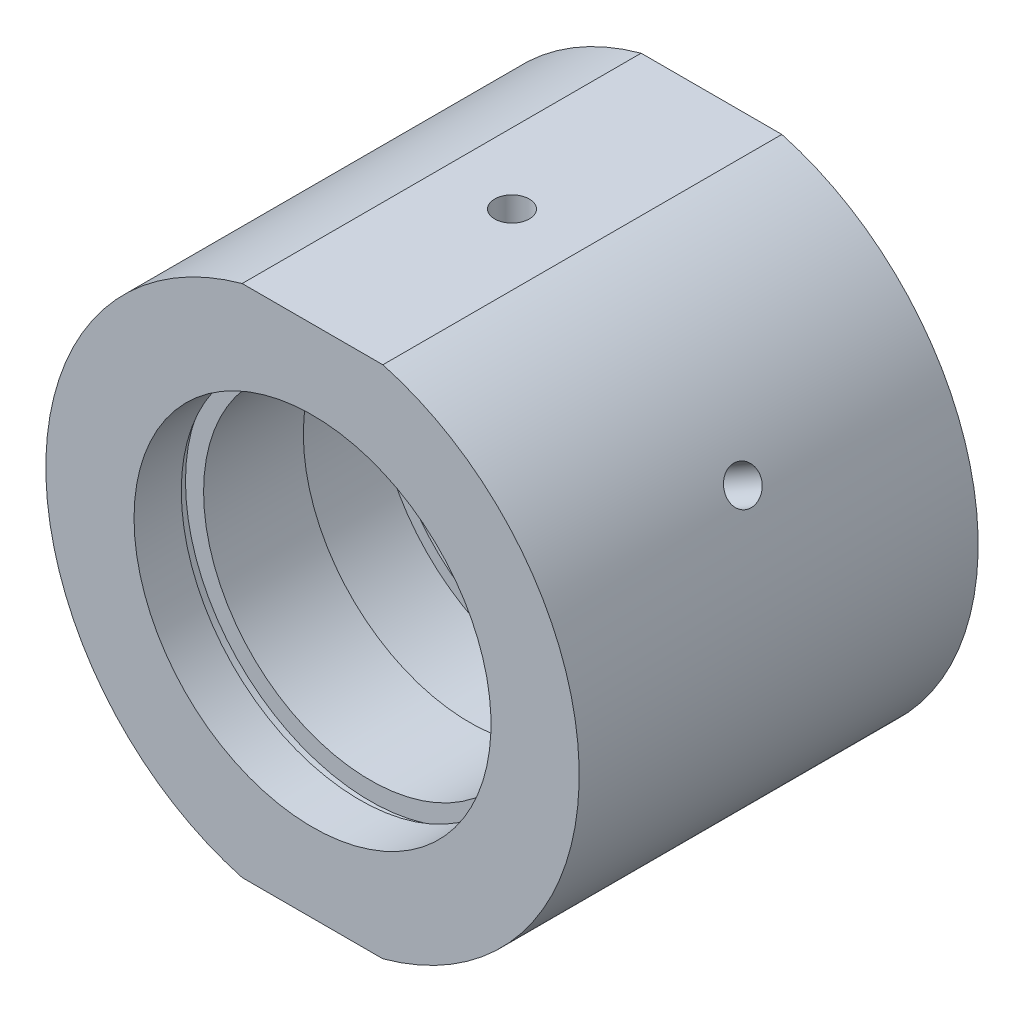
SolidWorks part; units mm, degrees
ref_plane "前视基准面" through (0, 0, 0) normal (0, 0, 1) x (1, 0, 0)
ref_plane "上视基准面" through (0, 0, 0) normal (0, 1, 0) x (1, 0, 0)
ref_plane "右视基准面" through (0, 0, 0) normal (1, 0, 0) x (0, 0, -1)
sketch "草图1" plane through (0, 0, 0) normal (0, 1, 0) x (1, 0, 0)
  line L0 (0, 31.9391) -> (0, -26.491) construction
  line L1 (25.4, 19) -> (25.4, -19)
  line L2 (25.4, -19) -> (17, -19)
  line L3 (17, -19) -> (17, -14.5)
  line L4 (17, -14.5) -> (17.6, -14.5)
  line L5 (17.6, -14.5) -> (17.6, -13.5)
  line L6 (17.6, -13.5) -> (15.875, -13.5)
  line L7 (15.875, -13.5) -> (15.875, -4)
  line L8 (15.875, -4) -> (16.975, -4)
  line L9 (16.975, -4) -> (16.975, 4)
  line L10 (16.975, 4) -> (15.875, 4)
  line L11 (15.875, 4) -> (15.875, 13.5)
  line L12 (15.875, 13.5) -> (17.6, 13.5)
  line L13 (17.6, 13.5) -> (17.6, 14.5)
  line L14 (17.6, 14.5) -> (17, 14.5)
  line L15 (17, 14.5) -> (17, 19)
  line L16 (17, 19) -> (25.4, 19)
  line L17 (25.4, 0) -> (-5.0345, 0) construction
  point P6 (16.975, 0)
  dimension "D1" = 38
  dimension "D2" = 16.975
  dimension "D3" = 15.875
  dimension "D4" = 15.875
  dimension "D5" = 17.6
  dimension "D6" = 17.6
  dimension "D7" = 17
  dimension "D8" = 17
  dimension "D9" = 25.4
  dimension "D10" = 1
  dimension "D11" = 1
  dimension "D12" = 5.5
  dimension "D13" = 5.5
  dimension "D14" = 8
  dimension "D15" = 4
  dimension "D16" = 19
  dimension "D17" = 15
  dimension "D18" = 0
revolve "旋转1" add sketch "草图1" angle 360 about L0
cosmetic thread "装饰螺纹线4" parameters "D1"=4.4999, "D2"=42
cosmetic thread "装饰螺纹线5" parameters "D1"=8, "D2"=35
sketch "草图2" plane through (0, 0, 19) normal (0, 0, 1) x (1, 0, 0)
  line L0 (0, 0) -> (43.1523, 0) construction
  line L1 (-33.152, 33.7489) -> (30.8698, 33.7489)
  line L2 (-33.152, 33.7489) -> (-33.152, 24.5)
  line L3 (-33.152, 24.5) -> (30.8698, 24.5)
  line L4 (30.8698, 33.7489) -> (30.8698, 24.5)
  line L5 (30.8698, -33.7489) -> (30.8698, -24.5)
  line L6 (-33.152, -24.5) -> (30.8698, -24.5)
  line L7 (-33.152, -33.7489) -> (-33.152, -24.5)
  line L8 (-33.152, -33.7489) -> (30.8698, -33.7489)
  circle A1 centre (0, 0) radius 25.4 construction
  dimension "D1" = 24.5
  dimension "D2" = 0.9
extrude "切除-拉伸1" cut sketch "草图2" against normal blind 49
sketch "草图10" plane through (0, 0, 0) normal (0, 0, 1) x (1, 0, 0)
  line L0 (0, 24.5) -> (0, -24.5)
  line L1 (6.7015, 24.5) -> (-6.7015, 24.5) construction
  line L2 (-6.7015, -24.5) -> (6.7015, -24.5) construction
  line L3 (0, 0) -> (-21.997, 12.7)
  line L4 (0, 0) -> (21.997, 12.7)
  line L5 (-25.4, 0) -> (0, 24.5)
  line L6 (0, -24.5) -> (3.1773, -24.5)
  circle A0 centre (0, 0) radius 25.4 construction
  circle A1 centre (0, 0) radius 25.4 construction
  arc A2 (-25.4, 0) -> (-21.997, 12.7) centre (0, 0) ccw
  arc A3 (21.997, 12.7) -> (-25.4, 0) centre (0, 0) ccw
  dimension "D1" = 60
  dimension "D2" = 60
hole_wizard "M4 螺纹孔2" positions "草图15" profile "草图16" tap size "M4" standard "ISO"
sketch "草图15" plane through (0, 24.5, 0) normal (0, 1, 0) x (1, 0, 0)
  point P0 (0, 0)
sketch "草图16" plane through (0, 24.5, 0) normal (1, 0, 0) x (0, 0, 1)
  line L0 (0, 0) -> (0, 6.4914)
  line L1 (0, 6.4914) -> (1.65, 5.5)
  line L2 (1.65, 5.5) -> (1.65, 0)
  line L5 (1.65, 0) -> (0, 0)
  line L10 (0, 6.4914) -> (-1.65, 5.5) construction
  line L11 (0, -6.35) -> (0, 107.95) construction
  dimension "螺纹孔钻头直径" = 3.3
  dimension "螺纹孔钻头深度" = 5.5
  dimension "导头角度" = 118
cosmetic thread "孔螺蚊线3" parameters "D1"=5.5, "D2"=4
hole_wizard "M6 螺纹孔2" positions "草图17" profile "草图18" tap size "M6" standard "ISO"
sketch "草图17" plane through (0, -24.5, 0) normal (0, -1, 0) x (-1, 0, 0)
  point P0 (0, 0)
sketch "草图18" plane through (0, -24.5, 0) normal (1, 0, 0) x (0, 0, -1)
  line L0 (0, 0) -> (0, 7.0022)
  line L1 (0, 7.0022) -> (2.5, 5.5)
  line L2 (2.5, 5.5) -> (2.5, 0)
  line L5 (2.5, 0) -> (0, 0)
  line L10 (0, 7.0022) -> (-2.5, 5.5) construction
  line L11 (0, -6.35) -> (0, 107.95) construction
  dimension "螺纹孔钻头直径" = 5
  dimension "螺纹孔钻头深度" = 5.5
  dimension "导头角度" = 118
cosmetic thread "孔螺蚊线4" parameters "D1"=5.5, "D2"=6
hole_wizard "M4 螺纹孔3" positions "3D草图10" profile "草图19" tap size "M4" standard "ISO"
sketch3d "3D草图10"
  point P0 (21.997, 12.7, 0)
  point P3 (-21.997, 12.7, 0)
  point P6 (-21.997, 12.7, 0)
  point P8 (-21.997, 12.7, 0)
  point P12 (21.997, 12.7, 0)
  point P15 (21.997, 12.7, 0)
cosmetic thread "孔螺蚊线5" parameters "D1"=8, "D2"=4
sketch "草图19" plane through (21.997, 12.7, 0) normal (0, 0, 1) x (-0.5, 0.866, 0)
  line L0 (0, 0) -> (0, 11.0914)
  line L1 (0, 11.0914) -> (1.65, 10.1)
  line L2 (1.65, 10.1) -> (1.65, 0)
  line L5 (1.65, 0) -> (0, 0)
  line L10 (0, 11.0914) -> (-1.65, 10.1) construction
  line L11 (0, -6.35) -> (0, 107.95) construction
  dimension "螺纹孔钻头直径" = 3.3
  dimension "螺纹孔钻头深度" = 10.1
  dimension "导头角度" = 118
cosmetic thread "孔螺蚊线6" parameters "D1"=8, "D2"=4
